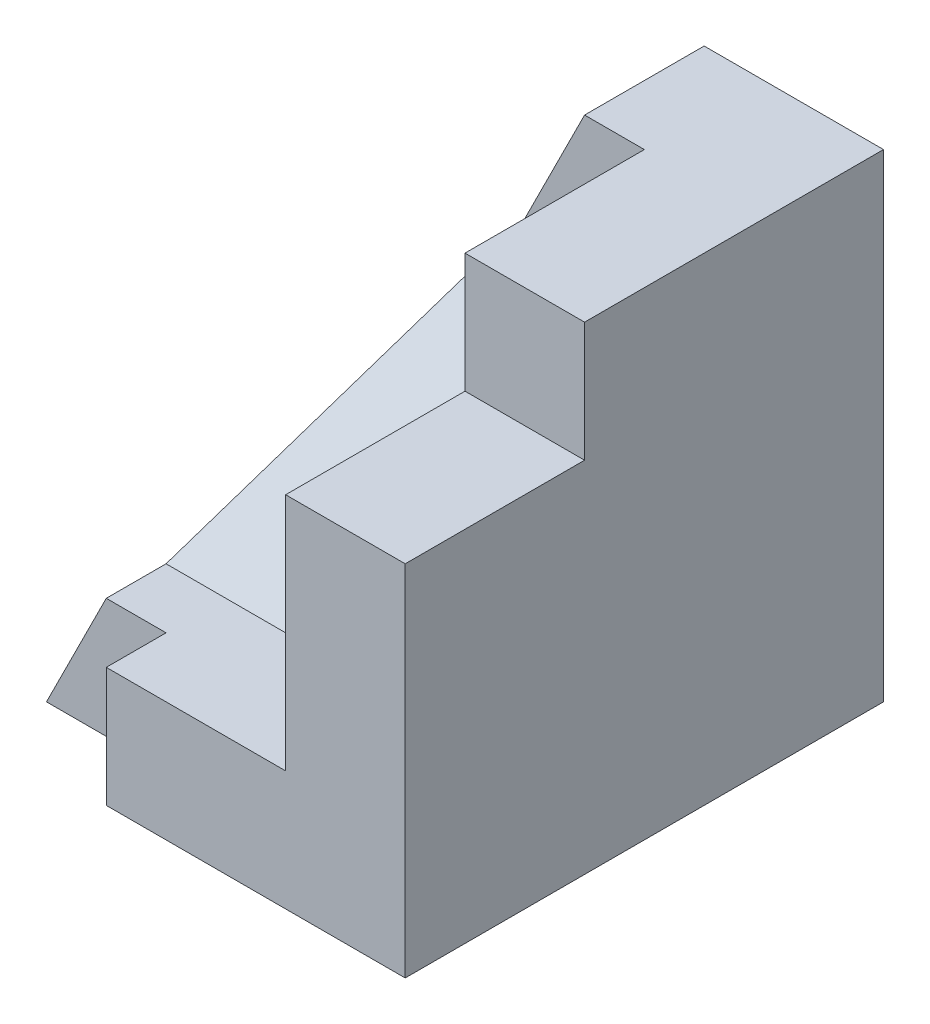
SolidWorks part; units mm, degrees
ref_plane "Front Plane" through (0, 0, 0) normal (0, 0, 1) x (1, 0, 0)
ref_plane "Top Plane" through (0, 0, 0) normal (0, 1, 0) x (1, 0, 0)
ref_plane "Right Plane" through (0, 0, 0) normal (1, 0, 0) x (0, 0, -1)
sketch "Sketch1" plane through (0, 0, 0) normal (0, 0, 1) x (1, 0, 0)
  line L1 (-17.5, 20) -> (17.5, 20)
  line L2 (-17.5, 20) -> (-17.5, -20)
  line L3 (-17.5, -20) -> (17.5, -20)
  line L4 (17.5, 20) -> (17.5, -20)
  line L5 (-17.5, 20) -> (17.5, -20) construction
  line L6 (-17.5, -20) -> (17.5, 20) construction
  point P0 (0, 0)
  dimension "D1" = 35
  dimension "D2" = 40
extrude "Boss-Extrude1" add sketch "Sketch1" along normal blind 40
sketch "Sketch2" plane through (0, 0, 40) normal (0, 0, 1) x (1, 0, 0)
  line L0 (17.5, 20) -> (17.5, 10)
  line L1 (17.5, -20) -> (17.5, 20) construction
  line L2 (17.5, 10) -> (7.5, 10)
  line L3 (7.5, 10) -> (7.5, 20)
  line L4 (17.5, 20) -> (-17.5, 20) construction
  line L5 (7.5, 20) -> (17.5, 20)
  dimension "D1" = 10
  dimension "D2" = 10
extrude "Cut-Extrude1" cut sketch "Sketch2" against normal blind 15
sketch "Sketch3" plane through (0, 0, 40) normal (0, 0, 1) x (1, 0, 0)
  line L0 (-7.5, -20) -> (-17.5, -20)
  line L1 (-17.5, -20) -> (17.5, -20) construction
  line L2 (-17.5, -20) -> (-17.5, -10)
  line L3 (-17.5, 20) -> (-17.5, -20) construction
  line L4 (-17.5, -10) -> (-7.5, -10)
  line L5 (-7.5, -10) -> (-7.5, -20)
  dimension "D1" = 10
  dimension "D2" = 10
extrude "Cut-Extrude2" cut sketch "Sketch3" against normal blind 5
sketch "Sketch4" plane through (0, 0, 40) normal (0, 0, 1) x (1, 0, 0)
  line L0 (-17.5, -10) -> (7.5, -10)
  line L1 (7.5, -10) -> (7.5, 20)
  line L2 (7.5, 20) -> (-17.5, 20)
  line L3 (-17.5, 20) -> (-17.5, -10)
extrude "Cut-Extrude3" cut sketch "Sketch4" against normal blind 10
sketch "Sketch5" plane through (0, 0, 30) normal (0, 0, 1) x (1, 0, 0)
  line L0 (2.5, 20) -> (-17.5, -20)
  line L1 (7.5, 20) -> (-17.5, 20) construction
  line L4 (-17.5, -20) -> (-17.5, 20)
  line L5 (-17.5, 20) -> (2.5, 20)
  dimension "D1" = 5
extrude "Cut-Extrude4" cut sketch "Sketch5" against normal through all
sketch "Sketch6" plane through (0, 0, 35) normal (0, 0, 1) x (1, 0, 0)
  line L0 (-12.5, -10) -> (-17.5, -20)
  line L1 (-7.5, -10) -> (-17.5, -10) construction
  line L2 (-17.5, -20) -> (-17.5, -10)
  line L3 (-17.5, -10) -> (-12.5, -10)
extrude "Cut-Extrude5" cut sketch "Sketch6" against normal blind 10
sketch "Sketch7" plane through (0, 0, 30) normal (0, 0, 1) x (1, 0, 0)
  line L0 (7.5, 20) -> (2.5, 20)
  line L1 (2.5, 20) -> (-2.5, 10)
  line L2 (-12.5, -10) -> (2.5, 20) construction
  line L3 (-2.5, 10) -> (7.5, 10)
  line L4 (7.5, 10) -> (7.5, 20) construction
  line L5 (7.5, 10) -> (7.5, 20)
  dimension "D1" = 10
extrude "Cut-Extrude6" cut sketch "Sketch7" against normal blind 20
sketch "Sketch11" plane through (0, 0, 30) normal (0, 0, 1) x (1, 0, 0)
  line L0 (-7.5, -10) -> (7.5, -10) construction
  point P0 (0, -10)
sketch "Sketch12" plane through (0, 0, 10) normal (0, 0, 1) x (1, 0, 0)
  point P0 (7.5, 10)
  point P1 (-2.5, 10)
ref_plane "Plane3" through (0, 10, 10) normal (0, 0.7071, 0.7071) x (1, 0, 0)
sketch "Sketch13" plane through (0, 10, 10) normal (0, 0.7071, 0.7071) x (1, 0, 0)
  line L0 (7.5, 0) -> (7.5, -28.2843)
  line L1 (7.5, -28.2843) -> (-12.5, -28.2843)
  line L2 (-12.5, -28.2843) -> (-2.5, 0)
  line L3 (-2.5, 0) -> (7.5, 0)
extrude "Cut-Extrude7" cut sketch "Sketch13" along normal blind 20
